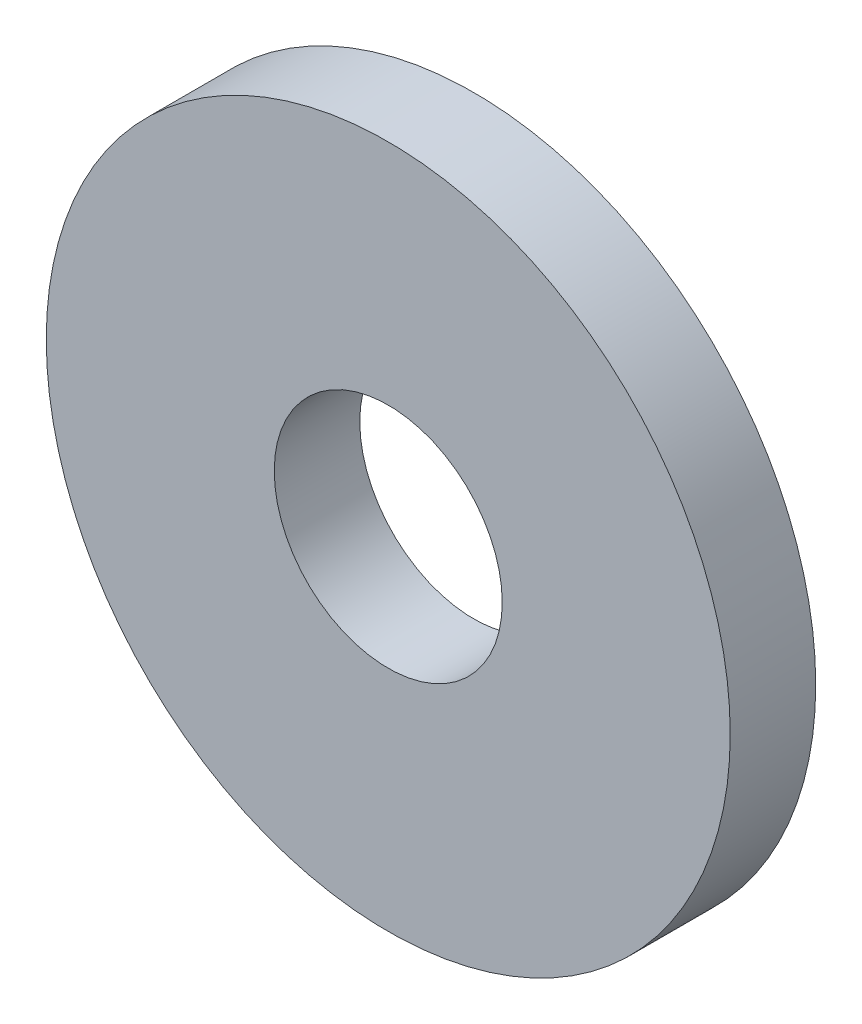
SolidWorks part; units mm, degrees
material "Teca"
ref_plane "Plano frontal" through (0, 0, 0) normal (0, 0, 1) x (1, 0, 0)
ref_plane "Plano superior" through (0, 0, 0) normal (0, 1, 0) x (1, 0, 0)
ref_plane "Plano direito" through (0, 0, 0) normal (1, 0, 0) x (0, 0, -1)
sketch "Esboço1" plane through (0, 0, 0) normal (0, 0, 1) x (1, 0, 0)
  circle A0 centre (0, 0) radius 2
  circle A1 centre (0, 0) radius 6
  dimension "D1" = 4
  dimension "D2" = 12
extrude "Ressalto-extrusão1" add sketch "Esboço1" along normal blind 1.5
